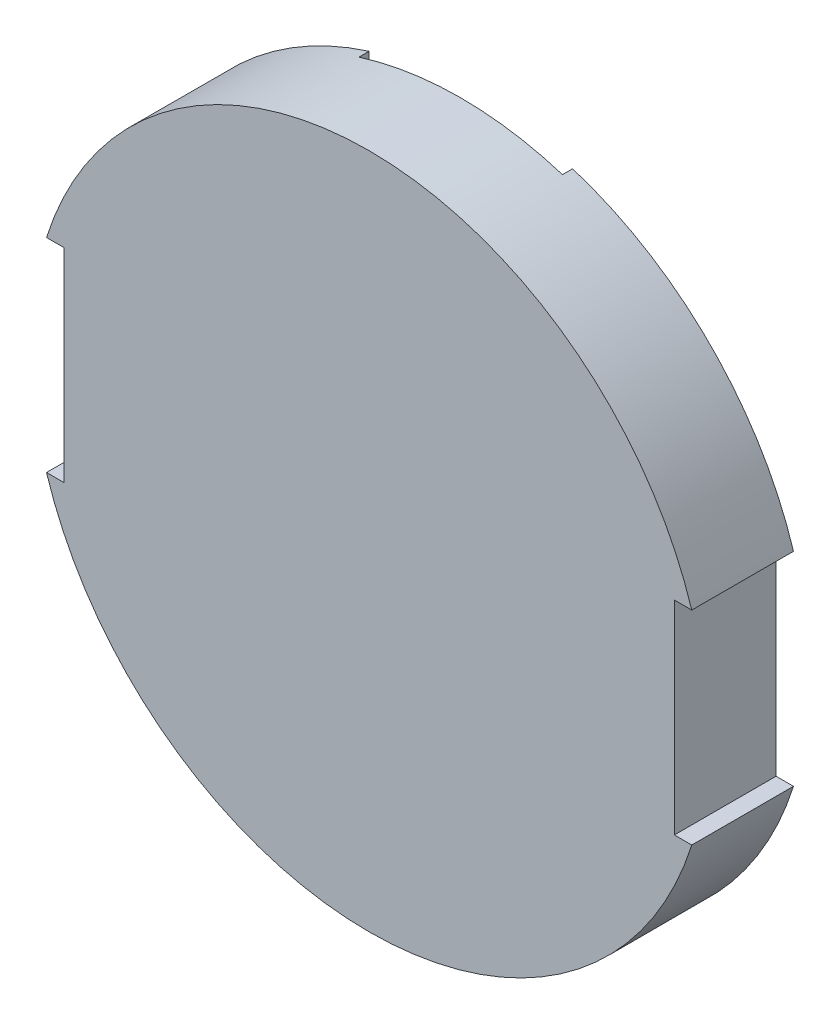
SolidWorks part; units mm, degrees
ref_plane "前基準面" through (0, 0, 0) normal (0, 0, 1) x (1, 0, 0)
ref_plane "上基準面" through (0, 0, 0) normal (0, 1, 0) x (1, 0, 0)
ref_plane "右基準面" through (0, 0, 0) normal (1, 0, 0) x (0, 0, -1)
sketch "草圖1" plane through (0, 0, 0) normal (0, 0, 1) x (1, 0, 0)
  line L0 (-63.4212, 20) -> (-60, 20)
  line L1 (-60, 20) -> (-60, -20)
  line L2 (0, 89.6109) -> (0, -98.3027) construction
  line L3 (-60, -20) -> (-63.4212, -20)
  line L4 (60, -20) -> (63.4212, -20)
  line L5 (63.4212, 20) -> (60, 20)
  line L6 (60, 20) -> (60, -20)
  circle A0 centre (0, 0) radius 66.5 construction
  arc A1 (-63.4212, 20) -> (63.4212, 20) centre (0, 0) cw
  arc A2 (-63.4212, -20) -> (63.4212, -20) centre (0, 0) ccw
  point P7 (-60, 0)
  point P13 (0, 0)
  point P16 (0, 0)
  dimension "D1" = 133
  dimension "D2" = 40
  dimension "D3" = 120
extrude "填料-伸長1" add sketch "草圖1" along normal blind 20
sketch "草圖2" plane through (0, 0, 0) normal (0, 0, -1) x (-1, 0, 0)
  line L0 (-20, 63.4212) -> (-20, -63.4212)
  line L2 (20, 63.4212) -> (20, -63.4212)
  line L3 (-22.0532, 0) -> (28.4046, 0) construction
  arc A0 (-20, 63.4212) -> (20, 63.4212) centre (0, 0) cw
  arc A1 (63.4212, 20) -> (-63.4212, 20) centre (0, 0) ccw construction
  arc A2 (-63.4212, -20) -> (63.4212, -20) centre (0, 0) ccw construction
  arc A3 (-20, -63.4212) -> (20, -63.4212) centre (0, 0) ccw
  point P7 (0, 66.5)
  dimension "D1" = 40
extrude "除料-伸長1" cut sketch "草圖2" against normal blind 2
